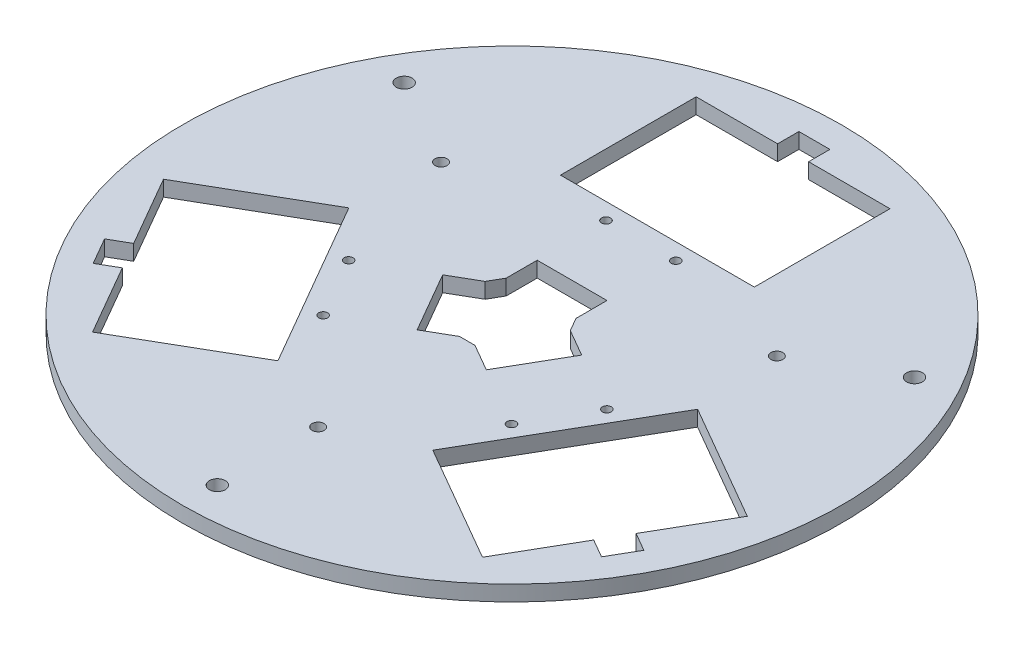
SolidWorks part; units mm, degrees
ref_plane "Front Plane" through (0, 0, 0) normal (0, 0, 1) x (1, 0, 0)
ref_plane "Top Plane" through (0, 0, 0) normal (0, 1, 0) x (1, 0, 0)
ref_plane "Right Plane" through (0, 0, 0) normal (1, 0, 0) x (0, 0, -1)
sketch "Sketch1" plane through (0, 0, 0) normal (0, 1, 0) x (1, 0, 0)
  line L5 (75.2868, -14.5994) -> (50.2868, -57.9006)
  line L6 (-25, 72.5) -> (25, 72.5)
  line L14 (-25, 72.5) -> (-25, 37.5)
  line L15 (-25, 37.5) -> (25, 37.5)
  line L16 (25, 72.5) -> (25, 37.5)
  line L17 (-25, 72.5) -> (25, 37.5) construction
  line L18 (-25, 37.5) -> (25, 72.5) construction
  line L19 (75.2868, -14.5994) -> (44.976, 2.9006)
  line L20 (44.976, 2.9006) -> (19.976, -40.4006)
  line L21 (50.2868, -57.9006) -> (19.976, -40.4006)
  line L22 (75.2868, -14.5994) -> (19.976, -40.4006) construction
  line L23 (44.976, 2.9006) -> (50.2868, -57.9006) construction
  line L24 (-50.2868, -57.9006) -> (-75.2868, -14.5994)
  line L25 (-50.2868, -57.9006) -> (-19.976, -40.4006)
  line L26 (-19.976, -40.4006) -> (-44.976, 2.9006)
  line L27 (-75.2868, -14.5994) -> (-44.976, 2.9006)
  line L28 (-50.2868, -57.9006) -> (-44.976, 2.9006) construction
  line L29 (-19.976, -40.4006) -> (-75.2868, -14.5994) construction
  line L30 (0, 0) -> (124.3802, 71.811) construction
  line L31 (0, 0) -> (0, 109.7125) construction
  line L32 (17.9234, 0.0442) -> (8.9234, -15.5442)
  line L33 (-9, 15.5) -> (9, 15.5)
  line L34 (-9, 15.5) -> (-9, 5.5)
  line L35 (-9, 5.5) -> (-7.1239, 5.5)
  line L36 (9, 15.5) -> (9, 5.5)
  line L37 (-9, 15.5) -> (9, 5.5) construction
  line L38 (-9, 5.5) -> (9, 15.5) construction
  line L39 (8.9234, -15.5442) -> (0.2631, -10.5442)
  line L40 (17.9234, 0.0442) -> (0.2631, -10.5442) construction
  line L41 (9.2631, 5.0442) -> (8.9234, -15.5442) construction
  line L42 (17.9234, 0.0442) -> (9.2631, 5.0442)
  line L43 (9.2631, 5.0442) -> (8.3251, 3.4195)
  line L44 (-8.9234, -15.5442) -> (-17.9234, 0.0442)
  line L45 (-17.9234, 0.0442) -> (-9.2631, 5.0442)
  line L46 (-8.9234, -15.5442) -> (-9.2631, 5.0442) construction
  line L47 (-0.2631, -10.5442) -> (-17.9234, 0.0442) construction
  line L48 (-8.9234, -15.5442) -> (-0.2631, -10.5442)
  line L49 (-0.2631, -10.5442) -> (-1.2012, -8.9195)
  line L50 (7.1239, 5.5) -> (9, 5.5)
  line L51 (-8.3251, 3.4195) -> (-9.2631, 5.0442)
  line L52 (1.2012, -8.9195) -> (0.2631, -10.5442)
  circle A0 centre (0, 0) radius 85
  arc A1 (-7.1239, 5.5) -> (-8.3251, 3.4195) centre (0, 0) ccw
  circle A2 centre (65.8179, 38) radius 2.05
  circle A3 centre (0, -76) radius 2.05
  circle A4 centre (-65.8179, 38) radius 2.05
  circle A5 centre (43.3013, 25) radius 1.55
  circle A6 centre (0, -50) radius 1.55
  circle A7 centre (-43.3013, 25) radius 1.55
  arc A8 (-1.2012, -8.9195) -> (1.2012, -8.9195) centre (0, 0) ccw
  arc A9 (8.3251, 3.4195) -> (7.1239, 5.5) centre (0, 0) ccw
  point P3 (0, 55)
  point P10 (47.6314, -27.5)
  point P15 (-47.6314, -27.5)
  point P27 (0, 10.5)
  dimension "D1" = 170
  dimension "D9" = 18
  dimension "D11" = 4.1
  dimension "D15" = 76
  dimension "D16" = 3.1
  dimension "D17" = 50
  dimension "D19" = 50
  dimension "D20" = 50
  dimension "D2" = 50
  dimension "D3" = 35
  dimension "D4" = 0
  dimension "D6" = 3
  dimension "D7" = 55
  dimension "D5" = 55
  dimension "D8" = 55
  dimension "D10" = 60
  dimension "D12" = 76
  dimension "D14" = 76
  dimension "D21" = 10
  dimension "D22" = 22
  dimension "D23" = 18
  dimension "D25" = 22
  dimension "D26" = 22
  dimension "D13" = 3
  dimension "D18" = 3
  dimension "D24" = 3
extrude "Boss-Extrude1" add sketch "Sketch1" along normal mid plane 4
sketch "Sketch2" plane through (0, 2, 0) normal (0, 1, 0) x (1, 0, 0)
  circle A1 centre (-9, 33.25) radius 1.15
  circle A2 centre (9, 33.25) radius 1.15
  circle A3 centre (-33.2953, -8.8308) radius 1.15
  circle A7 centre (-24.2953, -24.4192) radius 1.15
  circle A8 centre (24.2954, -24.4192) radius 1.15
  circle A9 centre (33.2953, -8.8308) radius 1.15
extrude "Cut-Extrude1" cut sketch "Sketch2" against normal through all
sketch "Sketch3" plane through (0, 2, 0) normal (0, 1, 0) x (1, 0, 0)
  line L0 (9, 7.5) -> (-9, 7.5)
  line L1 (9, 5.5) -> (9, 15.5) construction
  line L2 (-9, 15.5) -> (-9, 5.5) construction
  line L3 (-9, 7.5) -> (-10.9952, 4.0442)
  line L4 (-9.2631, 5.0442) -> (-17.9234, 0.0442) construction
  line L5 (-10.9952, 4.0442) -> (-1.9952, -11.5442)
  line L6 (-8.9234, -15.5442) -> (-0.2631, -10.5442) construction
  line L7 (-1.9952, -11.5442) -> (1.9952, -11.5442)
  line L8 (0.2631, -10.5442) -> (8.9234, -15.5442) construction
  line L9 (1.9952, -11.5442) -> (10.9952, 4.0442)
  line L10 (17.9234, 0.0442) -> (9.2631, 5.0442) construction
  line L11 (10.9952, 4.0442) -> (9, 7.5)
  line L12 (-17.9234, 0.0442) -> (-8.9234, -15.5442) construction
  line L14 (9, 15.5) -> (-9, 15.5) construction
  dimension "D1" = 8
  dimension "D2" = 8
extrude "Cut-Extrude2" cut sketch "Sketch3" against normal up to next
sketch "Sketch4" plane through (0, 2, 0) normal (0, 1, 0) x (1, 0, 0)
  line L0 (64.7868, -32.7859) -> (69.55, -35.5359)
  line L1 (50.2868, -57.9006) -> (75.2868, -14.5994) construction
  line L2 (69.55, -35.5359) -> (65.55, -42.4641)
  line L3 (65.55, -42.4641) -> (60.7868, -39.7141)
  line L4 (60.7868, -39.7141) -> (64.7868, -32.7859)
  line L5 (19.976, -40.4006) -> (50.2868, -57.9006) construction
  line L6 (0, 0) -> (0, -71.7433) construction
  line L7 (0, 0) -> (-63.587, 36.712) construction
  line L8 (-60.7868, -39.7141) -> (-64.7868, -32.7859)
  line L9 (-65.55, -42.4641) -> (-60.7868, -39.7141)
  line L10 (-69.55, -35.5359) -> (-65.55, -42.4641)
  line L11 (-64.7868, -32.7859) -> (-69.55, -35.5359)
  line L12 (-4, 72.5) -> (-4, 78)
  line L13 (-4, 78) -> (4, 78)
  line L14 (4, 78) -> (4, 72.5)
  line L15 (4, 72.5) -> (-4, 72.5)
  dimension "D1" = 8
  dimension "D2" = 5.5
  dimension "D3" = 21
  dimension "D4" = 120
extrude "Cut-Extrude3" cut sketch "Sketch4" against normal up to next
